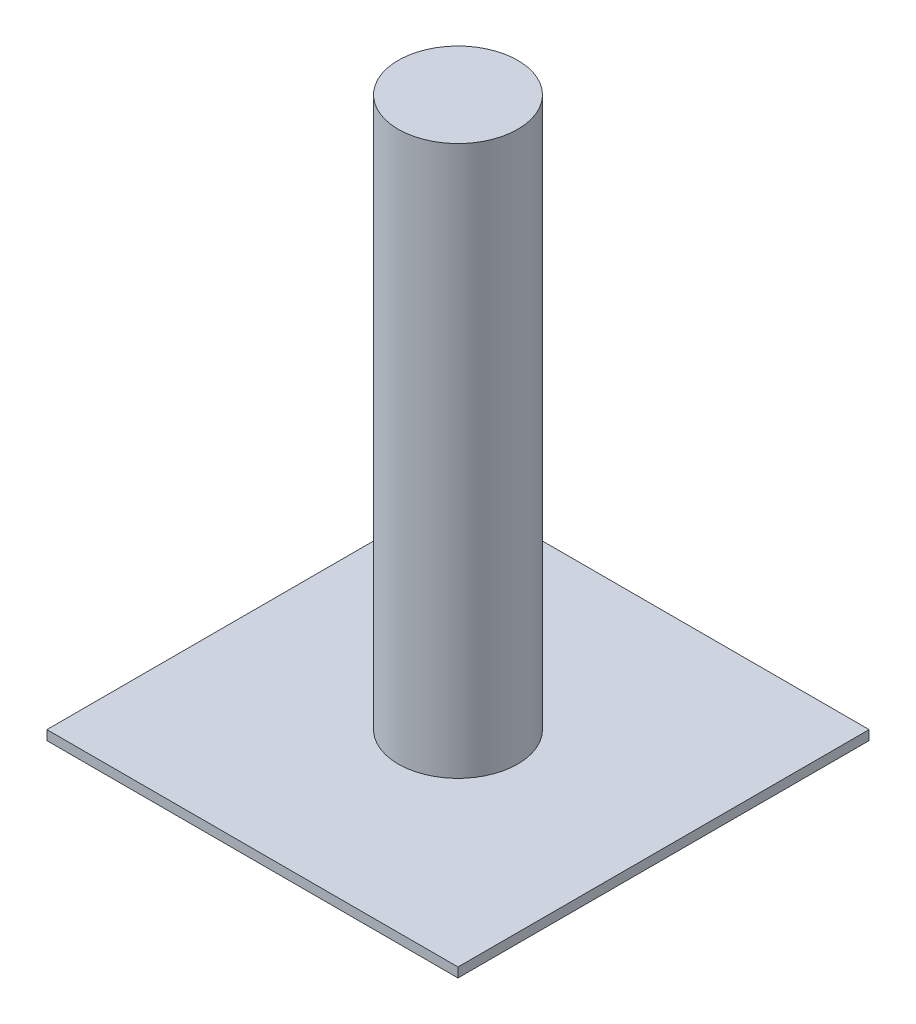
SolidWorks part; units mm, degrees
ref_plane "Front Plane" through (0, 0, 0) normal (0, 0, 1) x (1, 0, 0)
ref_plane "Top Plane" through (0, 0, 0) normal (0, 1, 0) x (1, 0, 0)
ref_plane "Right Plane" through (0, 0, 0) normal (1, 0, 0) x (0, 0, -1)
sketch "Sketch1" plane through (0, 0, 0) normal (0, 1, 0) x (1, 0, 0)
  line L1 (-43, 43) -> (43, 43)
  line L2 (-43, 43) -> (-43, -43)
  line L3 (-43, -43) -> (43, -43)
  line L4 (43, 43) -> (43, -43)
  line L5 (-43, 43) -> (43, -43) construction
  line L6 (-43, -43) -> (43, 43) construction
  point P0 (0, 0)
  dimension "D1" = 86
  dimension "D2" = 86
extrude "Boss-Extrude1" add sketch "Sketch1" along normal blind 2
sketch "Sketch2" plane through (0, 2, 0) normal (0, 1, 0) x (1, 0, 0)
  circle A0 centre (0, 0) radius 12.5
  dimension "D1" = 25
extrude "Boss-Extrude2" add sketch "Sketch2" along normal blind 115
